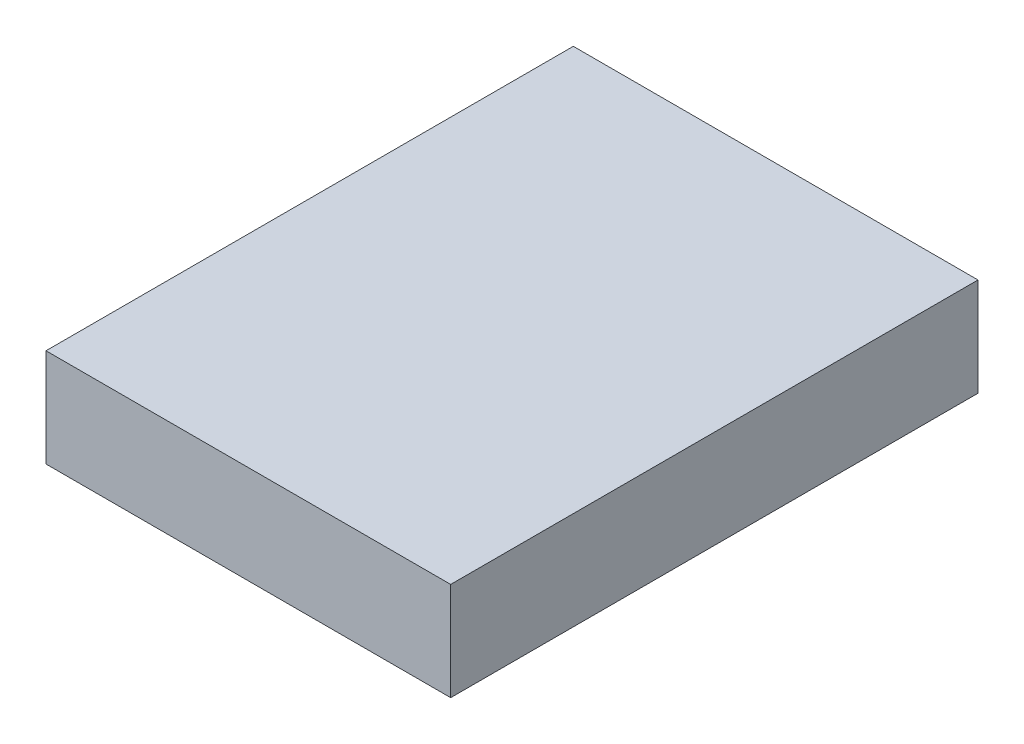
SolidWorks part; units mm, degrees
ref_plane "Front Plane" through (0, 0, 0) normal (0, 0, 1) x (1, 0, 0)
ref_plane "Top Plane" through (0, 0, 0) normal (0, 1, 0) x (1, 0, 0)
ref_plane "Right Plane" through (0, 0, 0) normal (1, 0, 0) x (0, 0, -1)
sketch "Sketch2" plane through (0, 0, 0) normal (0, 1, 0) x (1, 0, 0)
  line L1 (0, 0) -> (52.3875, 0)
  line L2 (0, 0) -> (0, 68.2625)
  line L3 (0, 68.2625) -> (52.3875, 68.2625)
  line L4 (52.3875, 0) -> (52.3875, 68.2625)
  dimension "D1" = 68.2625
  dimension "D2" = 52.3875
extrude "Boss-Extrude1" add sketch "Sketch2" along normal blind 12.7
